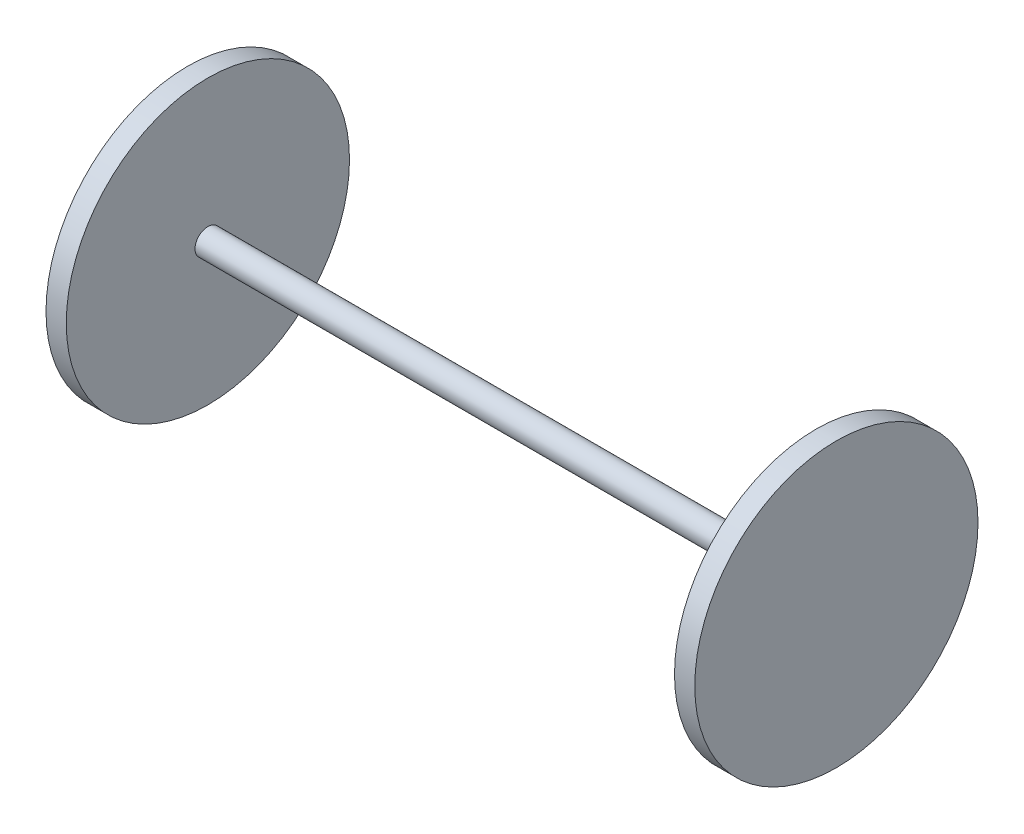
SolidWorks part; units mm, degrees
ref_plane "Front Plane" through (0, 0, 0) normal (0, 0, 1) x (1, 0, 0)
ref_plane "Top Plane" through (0, 0, 0) normal (0, 1, 0) x (1, 0, 0)
ref_plane "Right Plane" through (0, 0, 0) normal (1, 0, 0) x (0, 0, -1)
sketch "Sketch1" plane through (0, 0, 0) normal (1, 0, 0) x (0, 0, -1)
  circle A0 centre (0, 0) radius 3.175
  dimension "D1" = 6.35
extrude "Boss-Extrude1" add sketch "Sketch1" along normal mid plane 150
sketch "Sketch2" plane through (75, 0, 0) normal (1, 0, 0) x (0, 0, -1)
  circle A0 centre (0, 0) radius 34.925
  dimension "D1" = 69.85
extrude "Boss-Extrude2" add sketch "Sketch2" along normal blind 5
mirror "Mirror1" about plane through (0, 0, 0) normal (1, 0, 0) of "Boss-Extrude2"
